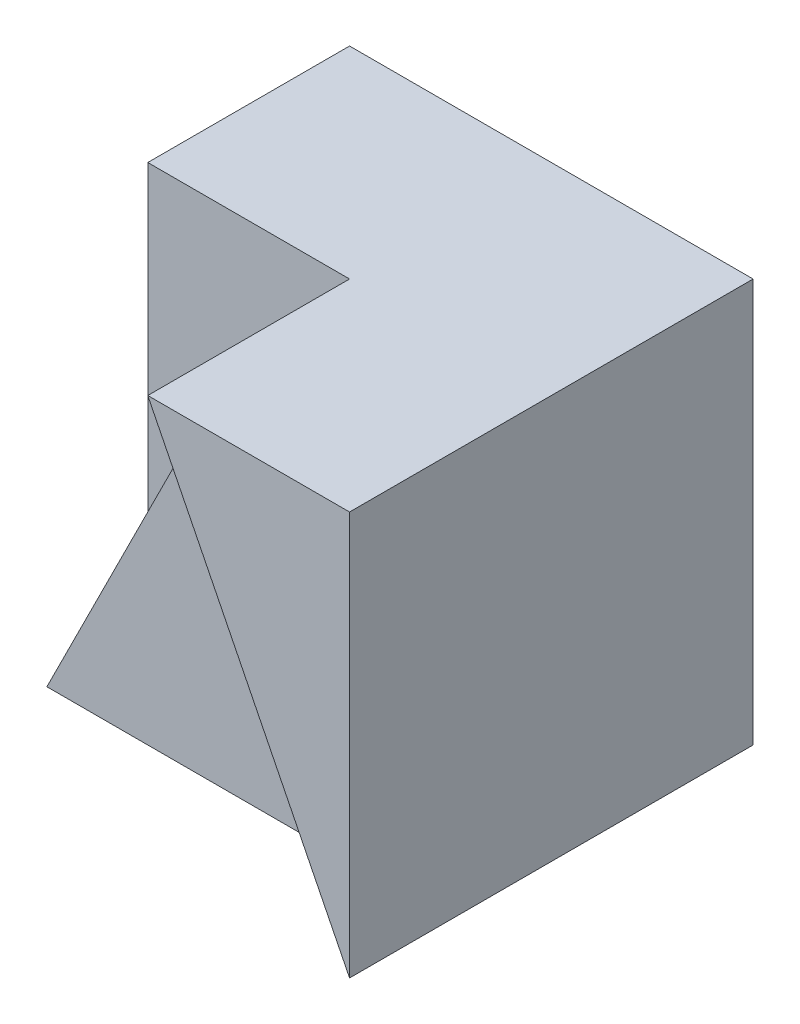
SolidWorks part; units mm, degrees
ref_plane "Front" through (0, 0, 0) normal (0, 0, 1) x (1, 0, 0)
ref_plane "Top" through (0, 0, 0) normal (0, 1, 0) x (1, 0, 0)
ref_plane "Right" through (0, 0, 0) normal (1, 0, 0) x (0, 0, -1)
sketch "Sketch1" plane through (0, 0, 0) normal (0, 1, 0) x (1, 0, 0)
  line L1 (-2, -2) -> (2, -2)
  line L2 (-2, -2) -> (-2, 2)
  line L3 (-2, 2) -> (2, 2)
  line L4 (2, -2) -> (2, 2)
  line L5 (-2, -2) -> (2, 2) construction
  line L6 (-2, 2) -> (2, -2) construction
  point P0 (0, 0)
  dimension "D1" = 4
  dimension "D2" = 4
extrude "Boss-Extrude1" add sketch "Sketch1" along normal blind 4
sketch "Sketch6" plane through (0, 0, 2) normal (0, 0, 1) x (1, 0, 0)
  line L0 (0, 4) -> (-2, 4)
  line L1 (-2, 4) -> (2, 4) construction
  line L2 (-2, 4) -> (-2, 0)
  line L3 (-2, 0) -> (0, 4)
extrude "Cut-Extrude3" cut sketch "Sketch6" against normal blind 2
sketch "Sketch7" plane through (0, 0, 2) normal (0, 0, 1) x (1, 0, 0)
  line L4 (0, 4) -> (-2, 0)
  line L5 (-2, 0) -> (2, 0)
  line L6 (2, 0) -> (0, 4)
extrude "Cut-Extrude4" cut sketch "Sketch7" against normal blind 1
